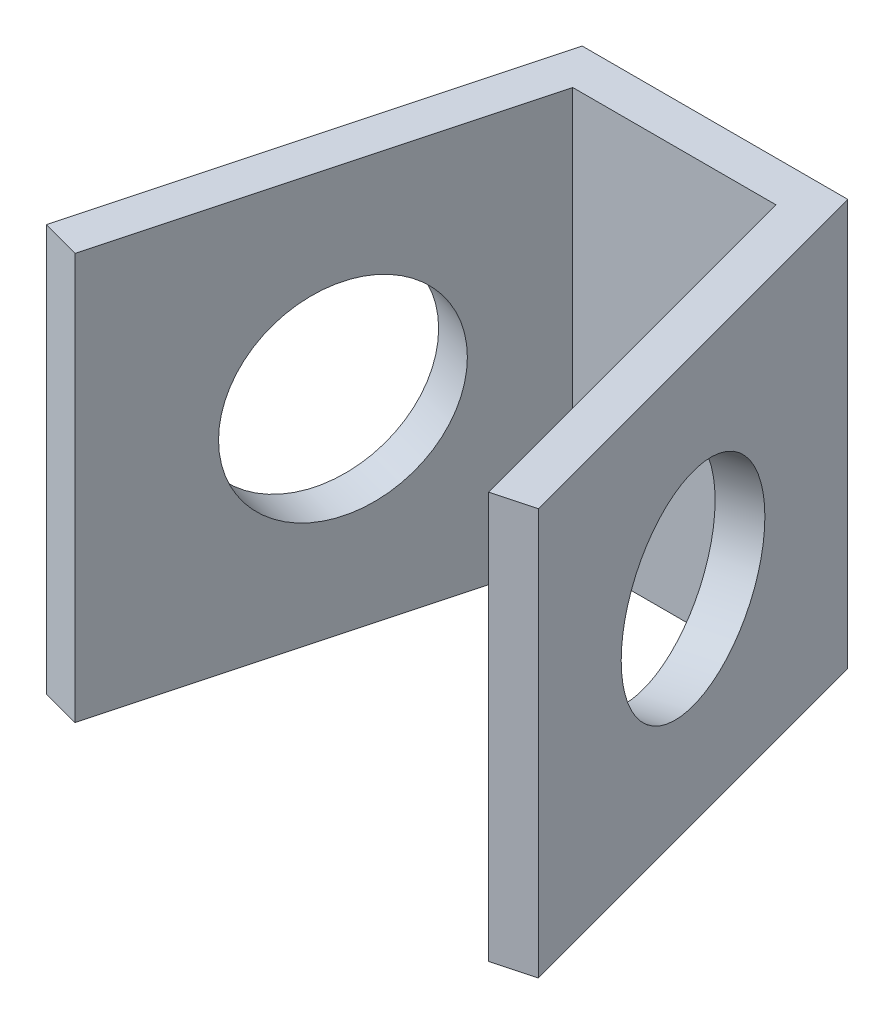
SolidWorks part; units mm, degrees
ref_plane "Ebene vorne" through (0, 0, 0) normal (0, 0, 1) x (1, 0, 0)
ref_plane "Ebene oben" through (0, 0, 0) normal (0, 1, 0) x (1, 0, 0)
ref_plane "Ebene rechts" through (0, 0, 0) normal (1, 0, 0) x (0, 0, -1)
sketch "Skizze1" plane through (0, 0, 0) normal (0, 1, 0) x (1, 0, 0)
  line L0 (-5, 0) -> (-10.1764, -19.3185)
  line L1 (-10.1764, -19.3185) -> (-12.1082, -18.8009)
  line L2 (-12.1082, -18.8009) -> (-6.5347, 2)
  line L3 (-5, 0) -> (5, 0)
  line L4 (-6.5347, 2) -> (6.5347, 2)
  line L5 (0, 2) -> (0, 0) construction
  line L6 (12.1082, -18.8009) -> (6.5347, 2)
  line L7 (10.1764, -19.3185) -> (12.1082, -18.8009)
  line L8 (5, 0) -> (10.1764, -19.3185)
  dimension "D1" = 2
  dimension "D2" = 10
  dimension "D3" = 20
  dimension "D4" = 30
extrude "Aufsatz-Linear austragen1" add sketch "Skizze1" along normal mid plane 20
sketch "Skizze2" plane through (6.5969, 0, -1.7676) normal (0.9659, 0, -0.2588) x (-0.2588, 0, -0.9659)
  line L0 (-21.2941, 0) -> (-10.5268, 0) construction
  line L1 (-21.2941, 10) -> (-21.2941, -10) construction
  line L2 (-10.5268, 0) -> (0.2406, 0) construction
  line L3 (0.2406, 10) -> (0.2406, -10) construction
  circle A0 centre (-10.5268, 0) radius 5
  dimension "D1" = 10
extrude "Schnitt-Linear austragen1" cut sketch "Skizze2" against normal up to next (2 mm away)
mirror "Spiegeln1" about plane through (0, 0, 0) normal (1, 0, 0) of "Schnitt-Linear austragen1"
